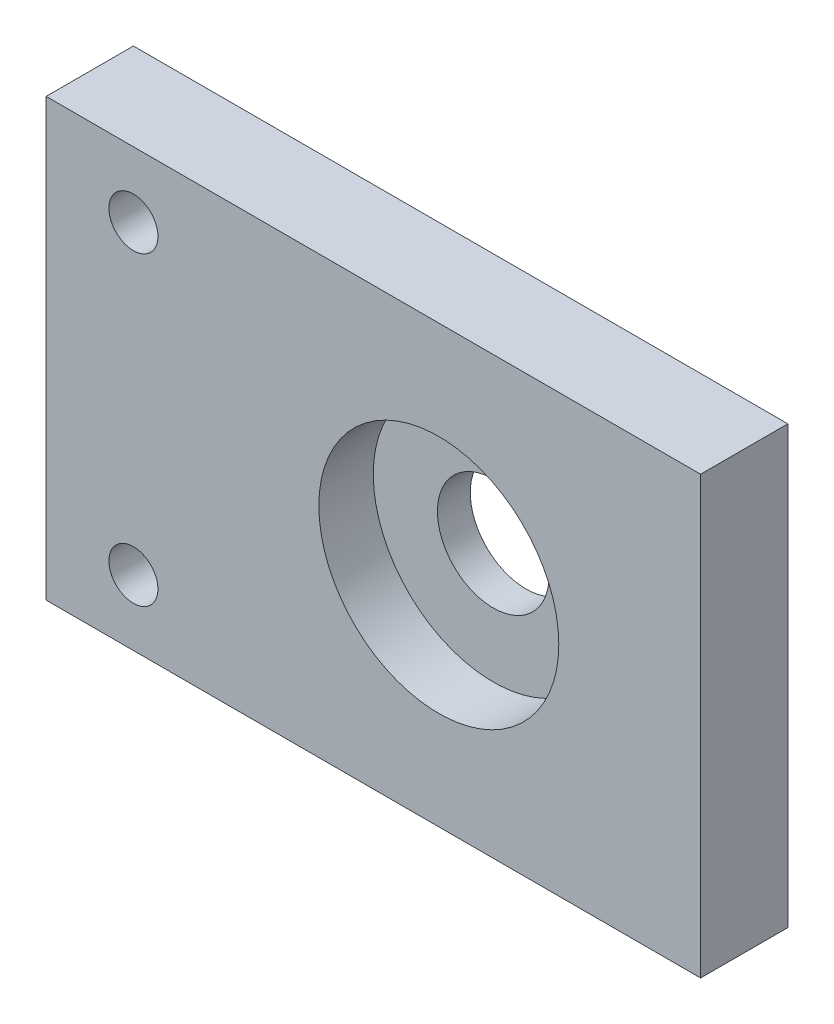
SolidWorks part; units mm, degrees
material "6061-T6 Al"
ref_plane "Front Plane" through (0, 0, 0) normal (0, 0, 1) x (1, 0, 0)
ref_plane "Top Plane" through (0, 0, 0) normal (0, 1, 0) x (1, 0, 0)
ref_plane "Right Plane" through (0, 0, 0) normal (1, 0, 0) x (0, 0, -1)
sketch "Sketch1" plane through (0, 0, 0) normal (0, 0, 1) x (1, 0, 0)
  line L1 (0, 0) -> (95.25, 0)
  line L2 (0, 0) -> (0, 63.5)
  line L3 (0, 63.5) -> (95.25, 63.5)
  line L4 (95.25, 0) -> (95.25, 63.5)
  dimension "D1" = 63.5
  dimension "D2" = 95.25
extrude "Boss-Extrude1" add sketch "Sketch1" along normal blind 12.7
hole_wizard "CBORE for 1/4 Socket Head Cap Screw1" positions "Sketch4" profile "Sketch3" counterbore size "1/4" standard "Ansi Inch" end condition through all
sketch "Sketch4" plane through (0, 0, 0) normal (0, 0, -1) x (-1, 0, 0)
  line L0 (-12.7, 9.525) -> (-12.7, 53.975) construction
  line L1 (0, 63.5) -> (0, 0) construction
  line L4 (0, 31.75) -> (-12.7, 31.75) construction
  line L5 (0, 63.5) -> (0, 0) construction
  point P0 (-12.7, 53.975)
  point P1 (-12.7, 9.525)
  dimension "D1" = 12.7
  dimension "D2" = 44.45
sketch "Sketch3" plane through (12.7, 53.975, 0) normal (1, 0, 0) x (0, 1, 0)
  line L0 (0, 0) -> (0, 12.7)
  line L1 (0, 12.7) -> (3.5712, 12.7)
  line L3 (3.5712, 12.7) -> (3.5712, 6.35)
  line L4 (3.5712, 6.35) -> (5.5562, 6.35)
  line L5 (5.5562, 6.35) -> (5.5562, 0)
  line L7 (5.5562, 0) -> (0, 0)
  line L11 (0, -6.35) -> (0, 107.95) construction
  dimension "Thru Hole Dia." = 7.1425
  dimension "Thru Hole Depth" = 12.7
  dimension "C'Bore Dia." = 11.1125
  dimension "C'Bore Depth" = 6.35
hole_wizard "CBORE for 5/8 Socket Head Cap Screw1" positions "Sketch6" profile "Sketch5" counterbore size "5/8" standard "Ansi Inch" end condition through all
sketch "Sketch6" plane through (0, 0, 12.7) normal (0, 0, 1) x (1, 0, 0)
  line L0 (95.25, 0) -> (95.25, 63.5) construction
  line L3 (95.25, 31.75) -> (57.15, 31.75) construction
  line L4 (95.25, 0) -> (95.25, 63.5) construction
  point P0 (57.15, 31.75)
  dimension "D1" = 38.1
sketch "Sketch5" plane through (57.15, 31.75, 12.7) normal (1, 0, 0) x (0, -1, 0)
  line L0 (0, 0) -> (0, 12.7)
  line L1 (0, 12.7) -> (8.128, 12.7)
  line L3 (8.128, 12.7) -> (8.128, 7.9248)
  line L4 (8.128, 7.9248) -> (17.4625, 7.9248)
  line L5 (17.4625, 7.9248) -> (17.4625, 0)
  line L7 (17.4625, 0) -> (0, 0)
  line L11 (0, -6.35) -> (0, 107.95) construction
  dimension "Thru Hole Dia." = 16.256
  dimension "Thru Hole Depth" = 12.7
  dimension "C'Bore Dia." = 34.925
  dimension "C'Bore Depth" = 7.9248
